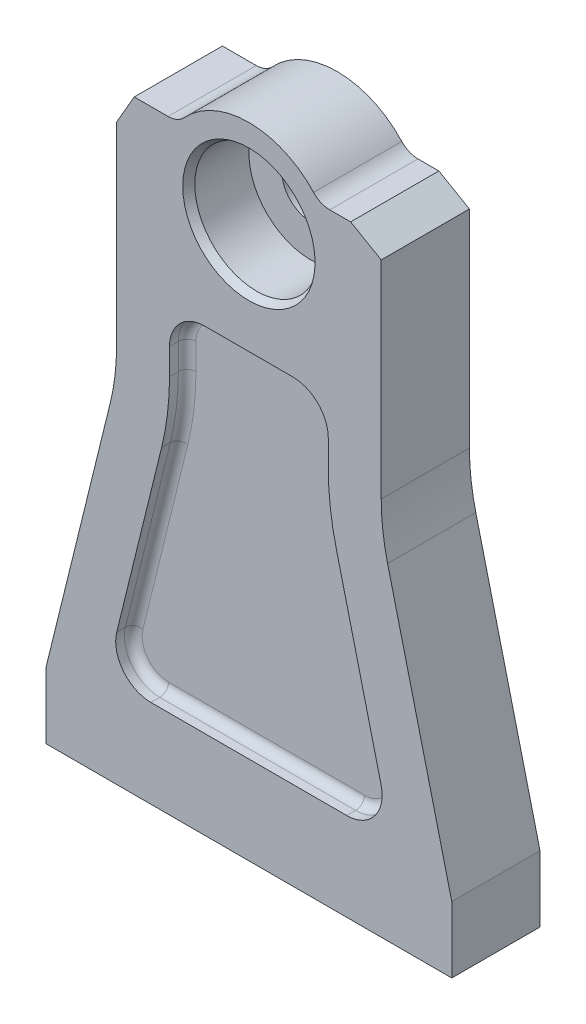
SolidWorks part; units mm, degrees
ref_plane "Front Plane" through (0, 0, 0) normal (0, 0, 1) x (1, 0, 0)
ref_plane "Top Plane" through (0, 0, 0) normal (0, 1, 0) x (1, 0, 0)
ref_plane "Right Plane" through (0, 0, 0) normal (1, 0, 0) x (0, 0, -1)
sketch "Sketch1" plane through (0, 0, 0) normal (0, 0, 1) x (1, 0, 0)
  line L0 (-46, 0) -> (46, 0)
  line L1 (46, 0) -> (46, 15)
  line L2 (46, 15) -> (31.4493, 74.1124)
  line L3 (16, 137) -> (30, 137)
  line L4 (30, 137) -> (30, 86.0633)
  line L5 (0, 0) -> (0, 72.6154) construction
  line L6 (-46, 0) -> (-46, 15)
  line L7 (-46, 15) -> (-31.4493, 74.1124)
  line L8 (-30, 137) -> (-30, 86.0633)
  line L9 (-16, 137) -> (-30, 137)
  circle A0 centre (0, 125) radius 6.5
  arc A1 (16, 137) -> (-16, 137) centre (0, 125) ccw
  arc A2 (31.4493, 74.1124) -> (30, 86.0633) centre (80, 86.0633) cw
  arc A3 (-31.4493, 74.1124) -> (-30, 86.0633) centre (-80, 86.0633) ccw
  point P17 (30, 80)
  point P20 (-30, 80)
  dimension "D2" = 13
  dimension "D3" = 40
  dimension "D9" = 50
  dimension "D1" = 125
  dimension "D4" = 46
  dimension "D5" = 15
  dimension "D6" = 65
  dimension "D7" = 12
  dimension "D8" = 30
extrude "Boss-Extrude1" add sketch "Sketch1" along normal mid plane 20
sketch "Sketch2" plane through (0, 0, 10) normal (0, 0, 1) x (1, 0, 0)
  circle A0 centre (0, 125) radius 14
  dimension "D1" = 28
extrude "Cut-Extrude1" cut sketch "Sketch2" against normal blind 14
chamfer "Chamfer1" distance 1 angle 60 1 edges at (14, 125, 10)
chamfer "Chamfer2" distance 4 angle 60 2 edges at (-30, 137, 0) (30, 137, 0)
fillet "Fillet1" radius 5 2 edges at (16, 137, 0) (-16, 137, 0)
sketch "Sketch3" plane through (0, 0, 10) normal (0, 0, 1) x (1, 0, 0)
  line L0 (-46, 0) -> (46, 0) construction
  line L15 (-18, 130.0718) -> (-18, 86.0633)
  line L16 (-19.7971, 71.2442) -> (-34.3478, 12.1318)
  line L17 (-18, 92) -> (-18, 86.0633)
  line L18 (-19.7971, 71.2442) -> (-29.9711, 29.9122)
  line L20 (-10, 100) -> (10, 100)
  line L21 (18, 86.0633) -> (18, 133)
  line L22 (34.3478, 12.1318) -> (19.7971, 71.2442)
  line L23 (18, 86.0633) -> (18, 92)
  line L24 (29.9711, 29.9122) -> (19.7971, 71.2442)
  line L25 (-46, 20) -> (46, 20)
  line L26 (-22.203, 20) -> (22.203, 20)
  arc A0 (29.9711, 29.9122) -> (22.203, 20) centre (22.203, 28) cw
  arc A1 (-22.203, 20) -> (-29.9711, 29.9122) centre (-22.203, 28) cw
  arc A2 (18, 92) -> (10, 100) centre (10, 92) ccw
  arc A3 (-18, 92) -> (-10, 100) centre (-10, 92) cw
  arc A7 (-19.7971, 71.2442) -> (-18, 86.0633) centre (-80, 86.0633) ccw
  arc A8 (-19.7971, 71.2442) -> (-18, 86.0633) centre (-80, 86.0633) ccw
  arc A10 (18, 86.0633) -> (19.7971, 71.2442) centre (80, 86.0633) ccw
  arc A11 (18, 86.0633) -> (19.7971, 71.2442) centre (80, 86.0633) ccw
  dimension "D5" = 8
  dimension "D4" = 100
  dimension "D1" = 12
  dimension "D2" = 12
  dimension "D3" = 20
extrude "Cut-Extrude2" cut sketch "Sketch3" against normal blind 4
fillet "Fillet2" radius 2 12 edges at (0, 20, 6) (-28.4997, 23.0653, 6) (-24.8841, 50.5782, 6) (-18.4509, 78.5995, 6) (-18, 89.0317, 6) (-15.6569, 97.6569, 6) (0, 100, 6) (15.6569, 97.6569, 6) (18, 89.0317, 6) (18.4509, 78.5995, 6) (24.8841, 50.5782, 6) (28.4997, 23.0653, 6)
mirror "Mirror1" about plane through (0, 0, 0) normal (0, 0, 1) of "Cut-Extrude2", "Fillet2"
hole_wizard "M10x1.25 Tapped Hole1" positions "Sketch7" profile "Sketch8" tap size "M10x1.25" standard "ISO"
sketch "Sketch7" plane through (0, 0, 0) normal (0, -1, 0) x (-1, 0, 0)
  line L0 (46, -10) -> (46, 10) construction
  line L1 (46, 10) -> (-46, 10) construction
  point P0 (30, 0)
  point P2 (-30, 0)
  point P11 (29.9883, -1.9804)
  point P12 (0, 0)
  dimension "D1" = 60
  dimension "D2" = 16
  dimension "D3" = 10
sketch "Sketch8" plane through (-30, 0, 0) normal (1, 0, 0) x (0, 0, -1)
  line L0 (0, 0) -> (0, 22.6438)
  line L1 (0, 22.6438) -> (4.4, 20)
  line L2 (4.4, 20) -> (4.4, 0)
  line L5 (4.4, 0) -> (0, 0)
  line L10 (0, 22.6438) -> (-4.4, 20) construction
  line L11 (0, -6.35) -> (0, 107.95) construction
  dimension "Tap Drill Dia." = 8.8
  dimension "Tap Drill Depth" = 20
  dimension "Drill Angle" = 118
cosmetic thread "Hole Thread1" parameters "D1"=20, "D2"=10
cosmetic thread "Hole Thread2" parameters "D1"=20, "D2"=10
